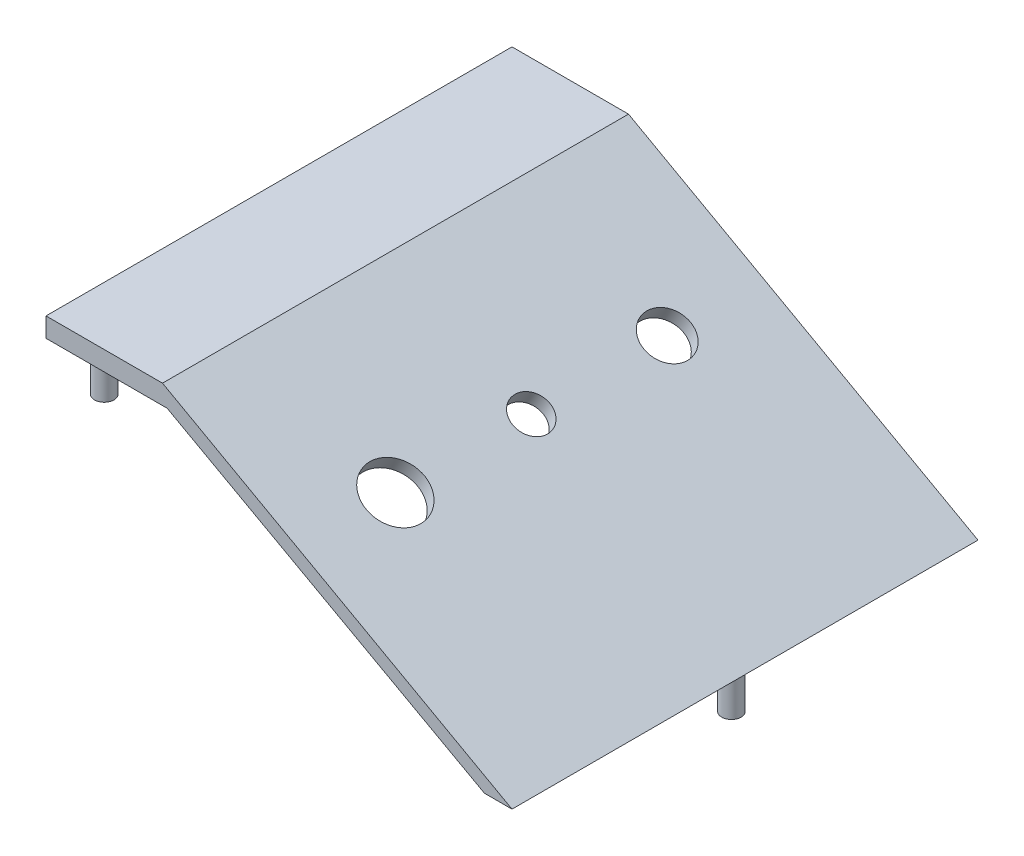
SolidWorks part; units mm, degrees
ref_plane "Front Plane" through (0, 0, 0) normal (0, 0, 1) x (1, 0, 0)
ref_plane "Top Plane" through (0, 0, 0) normal (0, 1, 0) x (1, 0, 0)
ref_plane "Right Plane" through (0, 0, 0) normal (1, 0, 0) x (0, 0, -1)
sketch "Sketch1" plane through (0, 0, 0) normal (0, 0, 1) x (1, 0, 0)
  line L0 (0, 0) -> (0, 76.2)
  line L1 (0, 76.2) -> (152.4, 76.2)
  line L2 (152.4, 76.2) -> (152.4, 0)
  line L3 (152.4, 0) -> (0, 0)
  dimension "D1" = 76.2
  dimension "D2" = 152.4
extrude "Boss-Extrude1" add sketch "Sketch1" along normal blind 152.4
sketch "Sketch2" plane through (0, 0, 152.4) normal (0, 0, 1) x (1, 0, 0)
  line L0 (152.4, 76.2) -> (38.1, 76.2)
  line L1 (152.4, 76.2) -> (0, 76.2) construction
  line L2 (38.1, 76.2) -> (152.4, 12.7)
  line L3 (152.4, 0) -> (152.4, 76.2) construction
  line L4 (152.4, 12.7) -> (152.4, 76.2)
  dimension "D1" = 114.3
  dimension "D2" = 63.5
extrude "Cut-Extrude1" cut sketch "Sketch2" against normal blind 152.4
sketch "Sketch4" plane through (0, 0, 152.4) normal (0, 0, 1) x (1, 0, 0)
  line L2 (39.6254, 69.85) -> (146.05, 11.2302)
  line L3 (146.05, 11.2302) -> (146.05, 0)
  line L4 (0, 0) -> (152.4, 0) construction
  line L9 (152.4, 0) -> (152.4, 12.7) construction
  line L11 (39.6254, 69.85) -> (0, 69.85)
  line L12 (0, 76.2) -> (0, 0) construction
  line L13 (0, 69.85) -> (0, 0)
  line L14 (0, 0) -> (146.05, 0)
  dimension "D4" = 6.35
extrude "Cut-Extrude4" cut sketch "Sketch4" against normal blind 152.4
sketch "Sketch6" plane through (41.3349, 74.4028, 0) normal (0.4856, 0.8742, 0) x (0.8742, -0.4856, 0)
  line L0 (-3.7006, -152.4) -> (127.0539, -152.4) construction
  line L1 (-3.7006, 0) -> (127.0539, 0) construction
  line L2 (-3.7006, 0) -> (-3.7006, -152.4) construction
  circle A0 centre (47.0994, -120.65) radius 9.525
  circle A1 centre (47.0994, -76.2) radius 6.096
  circle A2 centre (47.0994, -31.75) radius 7.62
  dimension "D1" = 19.05
  dimension "D2" = 12.192
  dimension "D3" = 15.24
  dimension "D4" = 31.75
  dimension "D6" = 44.45
  dimension "D7" = 50.8
  dimension "D8" = 50.8
  dimension "D9" = 50.8
  dimension "D5" = 31.75
extrude "Cut-Extrude5" cut sketch "Sketch6" against normal blind 25.4
sketch "Sketch7" plane through (0, 69.85, 0) normal (0, -1, 0) x (1, 0, 0)
  line L0 (39.6254, 0) -> (0, 0) construction
  line L1 (0, 0) -> (0, 152.4) construction
  line L2 (39.6254, 152.4) -> (0, 152.4) construction
  circle A0 centre (12.7, 6.35) radius 3.175
  circle A1 centre (12.7, 146.05) radius 3.175
  dimension "D1" = 6.35
  dimension "D2" = 6.35
  dimension "D3" = 6.35
  dimension "D4" = 12.7
  dimension "D6" = 12.7
  dimension "D5" = 6.35
extrude "Boss-Extrude2" add sketch "Sketch7" along normal blind 12.7
sketch "Sketch8" plane through (0, 0, 152.4) normal (0, 0, 1) x (1, 0, 0)
  line L0 (152.4, 12.7) -> (143.3816, 12.7)
  line L1 (146.05, 11.2302) -> (39.6254, 69.85) construction
  line L2 (143.3816, 12.7) -> (143.3816, 0)
  line L3 (143.3816, 0) -> (152.4, 0)
  line L4 (152.4, 0) -> (152.4, 12.7)
extrude "Cut-Extrude6" cut sketch "Sketch8" against normal blind 152.4
sketch "Sketch9" plane through (0, 12.7, 0) normal (0, -1, 0) x (1, 0, 0)
  line L0 (152.4, 152.4) -> (143.3816, 152.4) construction
  line L1 (152.4, 0) -> (152.4, 152.4) construction
  circle A0 centre (147.955, 76.2) radius 3.175
  dimension "D2" = 6.35
  dimension "D1" = 76.2
  dimension "D3" = 4.445
extrude "Boss-Extrude3" add sketch "Sketch9" along normal blind 12.7
